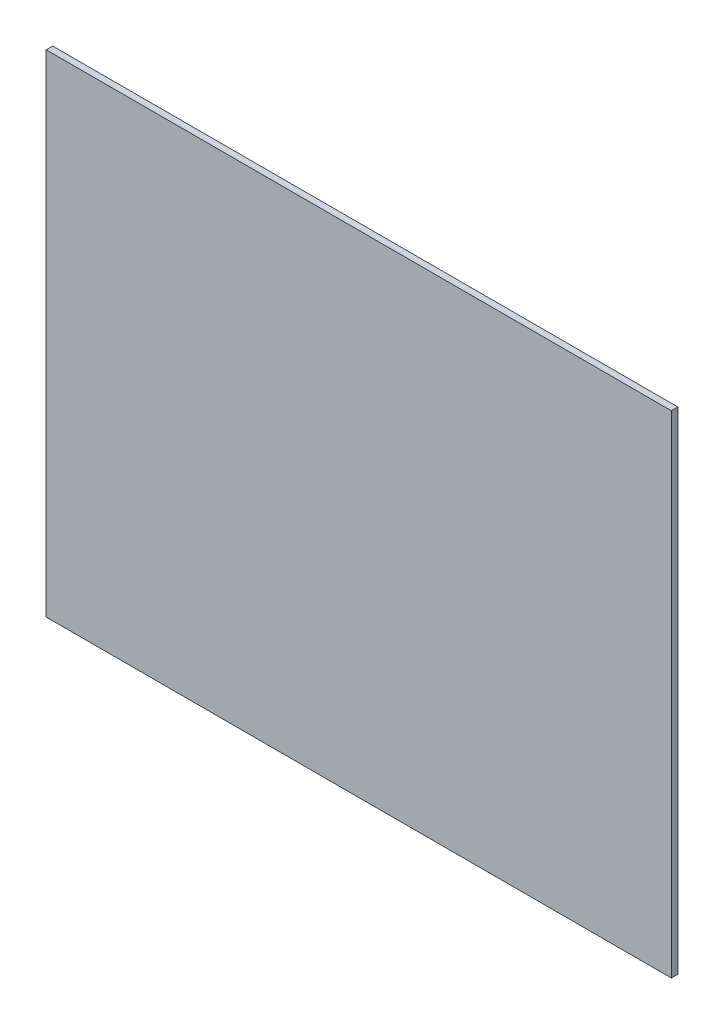
SolidWorks part; units mm, degrees
ref_plane "Front Plane" through (0, 0, 0) normal (0, 0, 1) x (1, 0, 0)
ref_plane "Top Plane" through (0, 0, 0) normal (0, 1, 0) x (1, 0, 0)
ref_plane "Right Plane" through (0, 0, 0) normal (1, 0, 0) x (0, 0, -1)
sketch "Sketch1" plane through (0, 0, 0) normal (0, 0, 1) x (1, 0, 0)
  line L1 (152.0875, -119.5) -> (-152.0875, -119.5)
  line L2 (152.0875, -119.5) -> (152.0875, 119.5)
  line L3 (152.0875, 119.5) -> (-152.0875, 119.5)
  line L4 (-152.0875, -119.5) -> (-152.0875, 119.5)
  line L5 (152.0875, -119.5) -> (-152.0875, 119.5) construction
  line L6 (152.0875, 119.5) -> (-152.0875, -119.5) construction
  point P0 (0, 0)
  dimension "D1" = 304.175
  dimension "D2" = 239
extrude "Boss-Extrude1" add sketch "Sketch1" along normal blind 3.175
